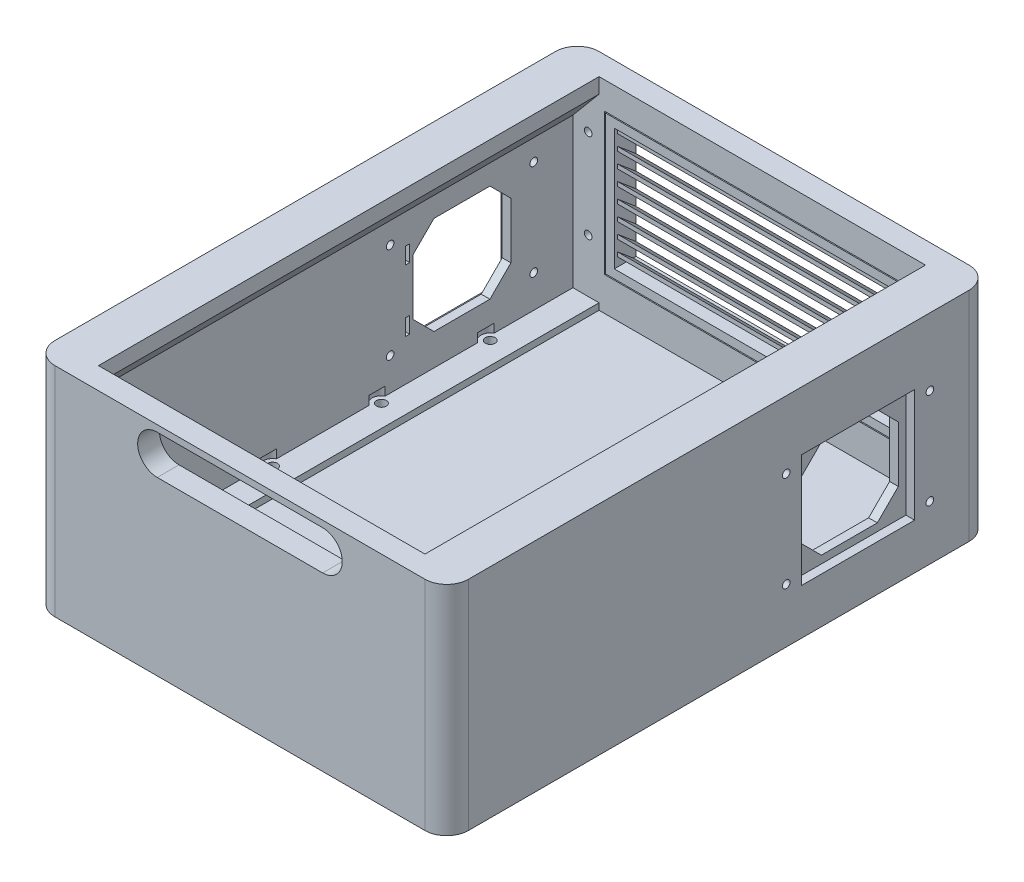
SolidWorks part; units mm, degrees
material "ABS"
ref_plane "Alzado" through (0, 0, 0) normal (0, 0, 1) x (1, 0, 0)
ref_plane "Planta" through (0, 0, 0) normal (0, 1, 0) x (1, 0, 0)
ref_plane "Vista lateral" through (0, 0, 0) normal (1, 0, 0) x (0, 0, -1)
sketch "Croquis1" plane through (0, 0, 0) normal (0, 1, 0) x (1, 0, 0)
  line L2 (0, 0) -> (190, 0)
  line L3 (0, 0) -> (0, 250)
  line L4 (0, 250) -> (190, 250)
  line L5 (190, 0) -> (190, 250)
  dimension "D1" = 250
  dimension "D2" = 190
extrude "Saliente-Extruir1" add sketch "Croquis1" along normal blind 100
shell "Vaciado1" thickness 10
sketch "Croquis2" plane through (0, 0, 0) normal (0, 0, 1) x (1, 0, 0)
  line L0 (57, 88) -> (133, 88) construction
  line L1 (57, 97) -> (133, 97)
  line L2 (57, 79) -> (133, 79)
  line L3 (0, 0) -> (190, 0) construction
  arc A0 (57, 97) -> (57, 79) centre (57, 88) ccw
  arc A1 (133, 79) -> (133, 97) centre (133, 88) ccw
  point P2 (95, 88)
  point P10 (95, 0)
  dimension "D1" = 76
  dimension "D2" = 18
  dimension "D3" = 88
extrude "Cortar-Extruir1" cut sketch "Croquis2" against normal up to next
fillet "Redondeo1" radius 10 4 edges at (0, 50, -250) (190, 50, -250) (0, 50, 0) (190, 50, 0)
sketch "Croquis5" plane through (10, 0, 0) normal (1, 0, 0) x (0, 0, -1)
  line L1 (10, 100) -> (240, 100)
  line L2 (10, 100) -> (10, 10)
  line L3 (10, 10) -> (240, 10)
  line L4 (240, 100) -> (240, 10)
extrude "Saliente-Extruir3" add sketch "Croquis5" along normal blind 10
sketch "Croquis6" plane through (180, 0, 0) normal (-1, 0, 0) x (0, 0, 1)
  line L1 (-240, 100) -> (-10, 100)
  line L2 (-240, 100) -> (-240, 10)
  line L3 (-240, 10) -> (-10, 10)
  line L4 (-10, 100) -> (-10, 10)
extrude "Saliente-Extruir4" add sketch "Croquis6" along normal blind 10
sketch "Croquis7" plane through (0, 0, 0) normal (0, -1, 0) x (1, 0, 0)
  line L0 (10, 0) -> (180, 0) construction
  line L1 (0, -240) -> (0, -10) construction
  line L2 (0, -125) -> (190, -125) construction
  line L3 (190, -10) -> (190, -240) construction
  line L4 (95, 0) -> (95, -250) construction
  line L5 (180, -250) -> (10, -250) construction
  circle A0 centre (10, -50) radius 2.25
  circle A1 centre (10, -100) radius 2.25
  circle A2 centre (10, -150) radius 2.25
  circle A3 centre (10, -200) radius 2.25
  circle A4 centre (180, -200) radius 2.25
  circle A5 centre (180, -150) radius 2.25
  circle A6 centre (180, -100) radius 2.25
  circle A7 centre (180, -50) radius 2.25
  dimension "D1" = 4.5
  dimension "D2" = 4.5
  dimension "D3" = 50
  dimension "D4" = 50
  dimension "D5" = 10
extrude "Cortar-Extruir3" cut sketch "Croquis7" against normal blind 10
sketch "Croquis10" plane through (0, 10, 0) normal (0, 1, 0) x (1, 0, 0)
  line L0 (180, 250) -> (10, 250) construction
  line L1 (85, 219.5) -> (105, 219.5)
  line L2 (85, 219.5) -> (85, 204.5)
  line L3 (85, 204.5) -> (105, 204.5)
  line L4 (105, 219.5) -> (105, 204.5)
  point P6 (95, 204.5)
  point P7 (95, 250)
  dimension "D1" = 20
  dimension "D2" = 15
  dimension "D3" = 30.5
extrude "Cortar-Extruir6" cut sketch "Croquis10" against normal through all
sketch "Croquis11" plane through (0, 10, 0) normal (0, 1, 0) x (1, 0, 0)
  line L0 (20, 10) -> (170, 10) construction
  line L1 (75, 10) -> (115, 10)
  line L2 (75, 10) -> (75, 70)
  line L3 (75, 70) -> (115, 70)
  line L4 (115, 10) -> (115, 70)
  line L5 (20, 10) -> (170, 10) construction
  point P6 (95, 70)
  point P9 (95, 10)
  dimension "D1" = 60
  dimension "D2" = 40
extrude "Cortar-Extruir7" cut sketch "Croquis11" against normal blind 7
sketch "Croquis13" plane through (0, 0, -250) normal (0, 0, -1) x (-1, 0, 0)
  line L0 (-180, 100) -> (-180, 0) construction
  line L1 (-167.5, 87.5) -> (-22.5, 87.5)
  line L2 (-167.5, 87.5) -> (-167.5, 22.5)
  line L3 (-167.5, 22.5) -> (-22.5, 22.5)
  line L4 (-22.5, 87.5) -> (-22.5, 22.5)
  line L17 (-10, 0) -> (-10, 100) construction
  line L18 (-180, 100) -> (-10, 100) construction
  line L19 (-180, 0) -> (-10, 0) construction
  dimension "D1" = 12.5
  dimension "D2" = 22.5
  dimension "D3" = 12.5
  dimension "D4" = 12.5
extrude "Cortar-Extruir8" cut sketch "Croquis13" against normal blind 10
sketch "Croquis14" plane through (0, 0, -250) normal (0, 0, -1) x (-1, 0, 0)
  line L0 (-22.5, 87.5) -> (-167.5, 87.5) construction
  line L1 (-170.5, 19.5) -> (-19.5, 19.5)
  line L2 (-170.5, 19.5) -> (-170.5, 90.5)
  line L3 (-170.5, 90.5) -> (-19.5, 90.5)
  line L4 (-19.5, 19.5) -> (-19.5, 90.5)
  line L5 (-167.5, 87.5) -> (-167.5, 22.5) construction
  line L6 (-167.5, 22.5) -> (-22.5, 22.5) construction
  line L7 (-22.5, 22.5) -> (-22.5, 87.5) construction
  dimension "D1" = 3
  dimension "D2" = 3
  dimension "D3" = 3
  dimension "D4" = 3
extrude "Cortar-Extruir9" cut sketch "Croquis14" against normal blind 5
sketch "Croquis15" plane through (0, 0, -245) normal (0, 0, -1) x (-1, 0, 0)
  line L0 (-19.5, 90.5) -> (-170.5, 90.5) construction
  line L1 (-170, 20) -> (-20, 20)
  line L2 (-170, 20) -> (-170, 90)
  line L3 (-170, 90) -> (-20, 90)
  line L4 (-20, 20) -> (-20, 90)
  line L5 (-170.5, 90.5) -> (-170.5, 19.5) construction
  line L6 (-19.5, 19.5) -> (-19.5, 90.5) construction
  line L7 (-170.5, 19.5) -> (-19.5, 19.5) construction
  dimension "D1" = 0.5
  dimension "D2" = 0.5
  dimension "D3" = 0.5
  dimension "D4" = 0.5
extrude "Saliente-Extruir5" add sketch "Croquis15" along normal blind 5 separate body
sketch "Croquis16" plane through (0, 0, -245) normal (0, 0, 1) x (1, 0, 0)
  line L0 (22.5, 87.5) -> (167.5, 87.5) construction
  line L1 (23, 23) -> (167, 23)
  line L2 (23, 23) -> (23, 87)
  line L3 (23, 87) -> (167, 87)
  line L4 (167, 23) -> (167, 87)
  line L5 (22.5, 22.5) -> (22.5, 87.5) construction
  line L6 (167.5, 87.5) -> (167.5, 22.5) construction
  line L7 (167.5, 22.5) -> (22.5, 22.5) construction
  dimension "D1" = 0.5
  dimension "D2" = 0.5
  dimension "D3" = 0.5
  dimension "D4" = 0.5
extrude "Saliente-Extruir6" add sketch "Croquis16" along normal blind 5
sketch "Croquis17" plane through (0, 0, -250) normal (0, 0, -1) x (-1, 0, 0)
  line L0 (-170, 90) -> (-170, 20) construction
  line L1 (-163, 27) -> (-27, 27)
  line L2 (-163, 27) -> (-163, 83)
  line L3 (-163, 83) -> (-27, 83)
  line L4 (-27, 27) -> (-27, 83)
  line L5 (-20, 90) -> (-170, 90) construction
  line L6 (-20, 20) -> (-20, 90) construction
  line L8 (-170, 20) -> (-20, 20) construction
  dimension "D1" = 7
  dimension "D2" = 7
  dimension "D3" = 7
  dimension "D4" = 7
extrude "Cortar-Extruir10" cut sketch "Croquis17" against normal blind 10
sketch "Croquis18" plane through (163, 0, 0) normal (-1, 0, 0) x (0, 0, 1)
  line L0 (-250, 74.8677) -> (-241.5, 82)
  line L1 (-250, 83) -> (-250, 27) construction
  line L3 (-241.5, 82) -> (-241.5, 80.0419)
  line L4 (-241.5, 80.0419) -> (-250, 72.9095)
  line L5 (-250, 72.9095) -> (-250, 74.8677)
  line L6 (-240, 100) -> (-240, 10) construction
  line L7 (-240, 83) -> (-250, 83) construction
  line L8 (-250, 65.9095) -> (-250, 67.8677)
  line L9 (-250, 67.8677) -> (-241.5, 75)
  line L10 (-241.5, 75) -> (-241.5, 73.0419)
  line L11 (-241.5, 73.0419) -> (-250, 65.9095)
  line L12 (-250, 58.9095) -> (-250, 60.8677)
  line L13 (-250, 60.8677) -> (-241.5, 68)
  line L14 (-241.5, 68) -> (-241.5, 66.0419)
  line L15 (-241.5, 66.0419) -> (-250, 58.9095)
  line L16 (-250, 51.9095) -> (-250, 53.8677)
  line L17 (-250, 53.8677) -> (-241.5, 61)
  line L18 (-241.5, 61) -> (-241.5, 59.0419)
  line L19 (-241.5, 59.0419) -> (-250, 51.9095)
  line L20 (-250, 44.9095) -> (-250, 46.8677)
  line L21 (-250, 46.8677) -> (-241.5, 54)
  line L22 (-241.5, 54) -> (-241.5, 52.0419)
  line L23 (-241.5, 52.0419) -> (-250, 44.9095)
  line L24 (-250, 37.9095) -> (-250, 39.8677)
  line L25 (-250, 39.8677) -> (-241.5, 47)
  line L26 (-241.5, 47) -> (-241.5, 45.0419)
  line L27 (-241.5, 45.0419) -> (-250, 37.9095)
  line L28 (-250, 30.9095) -> (-250, 32.8677)
  line L29 (-250, 32.8677) -> (-241.5, 40)
  line L30 (-241.5, 40) -> (-241.5, 38.0419)
  line L31 (-241.5, 38.0419) -> (-250, 30.9095)
  line L32 (-250, 23.9095) -> (-250, 25.8677)
  line L33 (-250, 25.8677) -> (-241.5, 33)
  line L34 (-241.5, 33) -> (-241.5, 31.0419)
  line L35 (-241.5, 31.0419) -> (-250, 23.9095)
  dimension "D1" = 1.5
  dimension "D2" = 50
  dimension "D3" = 1.5
  dimension "D4" = 1
  dimension "D5" = 8
extrude "Saliente-Extruir7" add sketch "Croquis18" along normal up to surface (136 mm away) up to face at (27, 55, -245)
sketch "Croquis19" plane through (0, 0, -250) normal (0, 0, -1) x (-1, 0, 0)
  line L0 (-170.5, 90.5) -> (-170.5, 19.5) construction
  line L1 (-170.5, 80) -> (-179.5, 80)
  line L2 (-170.5, 80) -> (-170.5, 71)
  line L3 (-170.5, 71) -> (-179.5, 71)
  line L4 (-179.5, 80) -> (-179.5, 71)
  line L5 (-19.5, 19.5) -> (-19.5, 90.5) construction
  line L6 (-170.5, 39) -> (-179.5, 39)
  line L7 (-170.5, 39) -> (-170.5, 30)
  line L8 (-170.5, 30) -> (-179.5, 30)
  line L9 (-179.5, 39) -> (-179.5, 30)
  line L10 (-19.5, 80) -> (-10.5, 80)
  line L11 (-19.5, 80) -> (-19.5, 71)
  line L12 (-19.5, 71) -> (-10.5, 71)
  line L13 (-10.5, 80) -> (-10.5, 71)
  line L14 (-19.5, 19.5) -> (-19.5, 90.5) construction
  line L15 (-19.5, 39) -> (-10.5, 39)
  line L16 (-19.5, 39) -> (-19.5, 30)
  line L17 (-19.5, 30) -> (-10.5, 30)
  line L18 (-10.5, 39) -> (-10.5, 30)
  line L19 (-20, 90) -> (-170, 90) construction
  line L20 (-170, 20) -> (-20, 20) construction
  dimension "D1" = 10
  dimension "D2" = 10
  dimension "D3" = 9
  dimension "D4" = 9
  dimension "D5" = 9
extrude "Cortar-Extruir11" cut sketch "Croquis19" against normal blind 3.25
sketch "Croquis20" plane through (0, 0, -250) normal (0, 0, -1) x (-1, 0, 0)
  line L0 (-170, 90) -> (-170, 20) construction
  line L1 (-170, 79.5) -> (-179, 79.5)
  line L2 (-170, 79.5) -> (-170, 71.5)
  line L3 (-170, 71.5) -> (-179, 71.5)
  line L4 (-179, 79.5) -> (-179, 71.5)
  line L5 (-20, 20) -> (-20, 90) construction
  line L6 (-170, 38.5) -> (-179, 38.5)
  line L7 (-170, 38.5) -> (-170, 30.5)
  line L8 (-170, 30.5) -> (-179, 30.5)
  line L9 (-179, 38.5) -> (-179, 30.5)
  line L10 (-20, 79.5) -> (-11, 79.5)
  line L11 (-20, 79.5) -> (-20, 71.5)
  line L12 (-20, 71.5) -> (-11, 71.5)
  line L13 (-11, 79.5) -> (-11, 71.5)
  line L14 (-170.5, 80) -> (-179.5, 80) construction
  line L15 (-20, 38.5) -> (-11, 38.5)
  line L16 (-20, 38.5) -> (-20, 30.5)
  line L17 (-20, 30.5) -> (-11, 30.5)
  line L18 (-11, 38.5) -> (-11, 30.5)
  line L19 (-179.5, 71) -> (-170.5, 71) construction
  line L20 (-179.5, 80) -> (-179.5, 71) construction
  line L21 (-170.5, 39) -> (-179.5, 39) construction
  line L23 (-179.5, 30) -> (-170.5, 30) construction
  dimension "D1" = 0.5
  dimension "D2" = 0.5
  dimension "D3" = 0.5
  dimension "D4" = 0.5
  dimension "D5" = 0.5
extrude "Saliente-Extruir8" add sketch "Croquis20" against normal blind 3
sketch "Croquis21" plane through (0, 0, -250) normal (0, 0, -1) x (-1, 0, 0)
  line L1 (-170, 79.5) -> (-179, 79.5) construction
  line L2 (-179, 79.5) -> (-179, 71.5) construction
  line L3 (-170, 38.5) -> (-179, 38.5) construction
  line L4 (-11, 71.5) -> (-11, 79.5) construction
  circle A0 centre (-175, 75.5) radius 1.75
  circle A1 centre (-175, 34.5) radius 1.75
  circle A2 centre (-15, 75.5) radius 1.75
  circle A3 centre (-15, 34.5) radius 1.75
  dimension "D1" = 3.5
  dimension "D2" = 4
  dimension "D3" = 4
  dimension "D4" = 4
  dimension "D5" = 4
extrude "Cortar-Extruir12" cut sketch "Croquis21" against normal blind 15
sketch "Croquis22" plane through (0, 0, -250) normal (0, 0, -1) x (-1, 0, 0)
  circle A0 centre (-175, 75.5) radius 2
  circle A1 centre (-175, 34.5) radius 2
  circle A2 centre (-15, 34.5) radius 2
  circle A3 centre (-15, 75.5) radius 2
  dimension "D1" = 4
  dimension "D2" = 4
  dimension "D3" = 4
  dimension "D4" = 4
extrude "Cortar-Extruir13" cut sketch "Croquis22" against normal blind 0.5
sketch "Croquis24" plane through (0, 0, -240) normal (0, 0, 1) x (1, 0, 0)
  line L0 (20, 93) -> (8, 78.699)
  line L1 (20, 10) -> (20, 100) construction
  line L2 (8, 78.699) -> (8, 10)
  line L8 (170, 100) -> (170, 10) construction
  line L11 (182, 10) -> (182, 78.699)
  line L12 (182, 78.699) -> (170, 93)
  line L13 (170, 93) -> (20, 93)
  line L15 (0, 100) -> (0, 0) construction
  line L17 (8, 10) -> (20, 10)
  line L18 (20, 10) -> (20, 7)
  line L19 (20, 7) -> (170, 7)
  line L20 (170, 7) -> (170, 10)
  line L21 (170, 10) -> (20, 10) construction
  line L22 (170, 10) -> (182, 10)
  line L23 (180, 0) -> (10, 0) construction
  line L24 (190, 0) -> (190, 100) construction
  line L26 (170, 100) -> (20, 100) construction
  dimension "D1" = 7
  dimension "D2" = 8
  dimension "D3" = 8
  dimension "D4" = 20
  dimension "D5" = 50
  dimension "D6" = 7
extrude "Cortar-Extruir14" cut sketch "Croquis24" along normal up to surface (230 mm away)
sketch "Croquis25" plane through (0, 0, 0) normal (-1, 0, 0) x (0, 0, 1)
  line L0 (-10, 93) -> (-240, 93) construction
  line L1 (-215, 73) -> (-163, 73)
  line L2 (-215, 73) -> (-215, 21)
  line L3 (-215, 21) -> (-163, 21)
  line L4 (-163, 73) -> (-163, 21)
  line L5 (-240, 100) -> (-240, 0) construction
  dimension "D1" = 52
  dimension "D2" = 52
  dimension "D3" = 20
  dimension "D4" = 25
sketch "Croquis26" plane through (0, 10, 0) normal (0, 1, 0) x (1, 0, 0)
  circle A0 centre (10, 200) radius 4.25
  circle A1 centre (10, 150) radius 4.25
  circle A2 centre (10, 100) radius 4.25
  circle A3 centre (10, 50) radius 4.25
  circle A4 centre (180, 50) radius 4.25
  circle A5 centre (180, 100) radius 4.25
  circle A6 centre (180, 150) radius 4.25
  circle A7 centre (180, 200) radius 4.25
  dimension "D1" = 8.5
extrude "Cortar-Extruir15" cut sketch "Croquis26" along normal blind 4
extrude "Cortar-Extruir16" cut sketch "Croquis25" against normal blind 4
sketch "Croquis28" plane through (4, 0, 0) normal (-1, 0, 0) x (0, 0, 1)
  line L8 (-211.5, 34.1447) -> (-211.5, 59.8553)
  line L9 (-211.5, 59.8553) -> (-201.8553, 69.5)
  line L10 (-201.8553, 69.5) -> (-176.1447, 69.5)
  line L11 (-176.1447, 69.5) -> (-166.5, 59.8553)
  line L12 (-166.5, 59.8553) -> (-166.5, 34.1447)
  line L13 (-166.5, 34.1447) -> (-176.1447, 24.5)
  line L14 (-176.1447, 24.5) -> (-201.8553, 24.5)
  line L15 (-201.8553, 24.5) -> (-211.5, 34.1447)
  line L17 (-163, 73) -> (-215, 73) construction
  line L18 (-163, 21) -> (-163, 73) construction
  dimension "D1" = 50
  dimension "D2" = 50
  dimension "D3" = 45
  dimension "D4" = 45
  dimension "D5" = 135
  dimension "D6" = 135
  dimension "D7" = 3.5
  dimension "D8" = 3.5
extrude "Cortar-Extruir17" cut sketch "Croquis28" against normal blind 4
sketch "Croquis29" plane through (0, 0, 0) normal (-1, 0, 0) x (0, 0, 1)
  line L0 (-163, 73) -> (-215, 73) construction
  line L1 (-215, 73) -> (-215, 21) construction
  line L2 (-163, 21) -> (-163, 73) construction
  line L3 (-215, 21) -> (-163, 21) construction
  circle A0 centre (-222, 69) radius 1.75
  circle A1 centre (-156, 69) radius 1.75
  circle A2 centre (-156, 25) radius 1.75
  circle A3 centre (-222, 25) radius 1.75
  dimension "D2" = 3.5
  dimension "D1" = 4
  dimension "D3" = 7
  dimension "D4" = 7
  dimension "D5" = 4
extrude "Cortar-Extruir18" cut sketch "Croquis29" against normal blind 8
ref_plane "Plano1" through (95, 0, 0) normal (-1, 0, 0) x (0, 0, 1)
mirror "Simetría1" about plane through (95, 0, 0) normal (-1, 0, 0) of "Cortar-Extruir16", "Cortar-Extruir17", "Cortar-Extruir18"
sketch "Croquis30" plane through (4, 0, 0) normal (-1, 0, 0) x (0, 0, 1)
  line L5 (-163, 21) -> (-163, 73) construction
  line L6 (-163, 65) -> (-165, 65)
  line L7 (-163, 65) -> (-163, 57.5)
  line L8 (-163, 57.5) -> (-165, 57.5)
  line L9 (-165, 65) -> (-165, 57.5)
  line L10 (-163, 21) -> (-163, 73) construction
  line L11 (-163, 36.5) -> (-165, 36.5)
  line L12 (-163, 36.5) -> (-163, 29)
  line L13 (-163, 29) -> (-165, 29)
  line L14 (-165, 36.5) -> (-165, 29)
  line L15 (-215, 21) -> (-163, 21) construction
  line L16 (-163, 73) -> (-215, 73) construction
  dimension "D1" = 2
  dimension "D2" = 2
  dimension "D3" = 8
  dimension "D4" = 8
  dimension "D5" = 7.5
  dimension "D6" = 7.5
extrude "Cortar-Extruir19" cut sketch "Croquis30" against normal blind 10
mirror "Simetría2" about plane through (95, 0, 0) normal (-1, 0, 0) of "Cortar-Extruir19"
